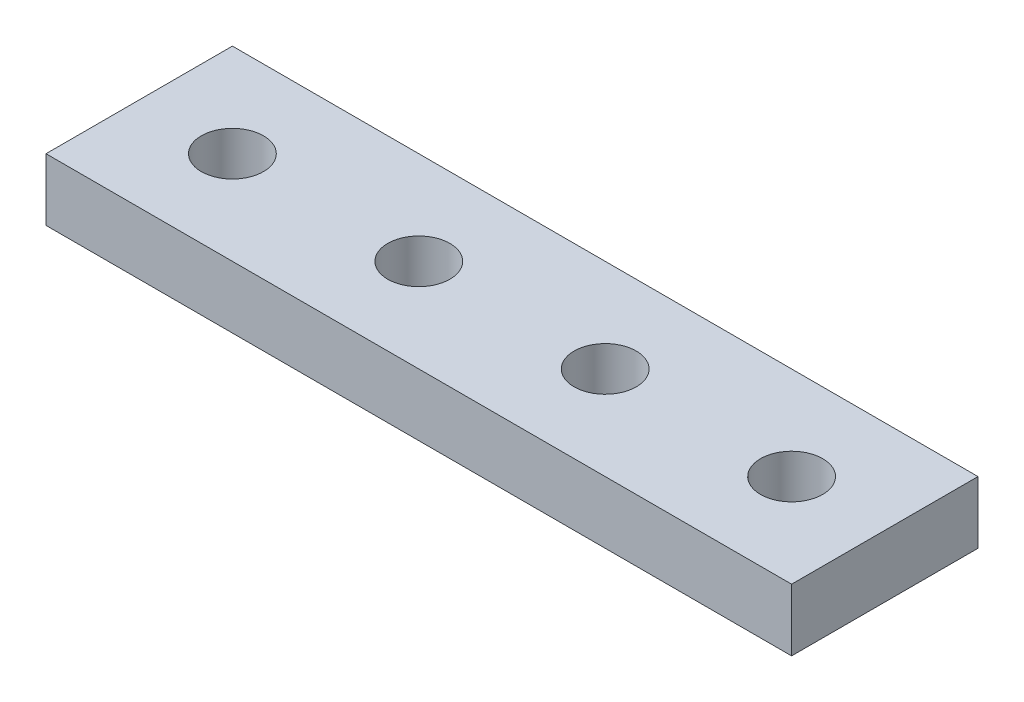
SolidWorks part; units mm, degrees
ref_plane "Front Plane" through (0, 0, 0) normal (0, 0, 1) x (1, 0, 0)
ref_plane "Top Plane" through (0, 0, 0) normal (0, 1, 0) x (1, 0, 0)
ref_plane "Right Plane" through (0, 0, 0) normal (1, 0, 0) x (0, 0, -1)
sketch "Sketch1" plane through (0, 0, 0) normal (0, 1, 0) x (1, 0, 0)
  line L1 (0, 0) -> (120, 0)
  line L2 (0, 0) -> (0, 30)
  line L3 (0, 30) -> (120, 30)
  line L4 (120, 0) -> (120, 30)
  circle A0 centre (15, 15) radius 5
  circle A1 centre (45, 15) radius 5
  circle A2 centre (75, 15) radius 5
  circle A3 centre (105, 15) radius 5
  dimension "D3" = 10
  dimension "D1" = 30
  dimension "D2" = 120
  dimension "D4" = 15
  dimension "D5" = 15
  dimension "D7" = 30
  dimension "D6" = 4
extrude "Boss-Extrude1" add sketch "Sketch1" along normal blind 10
